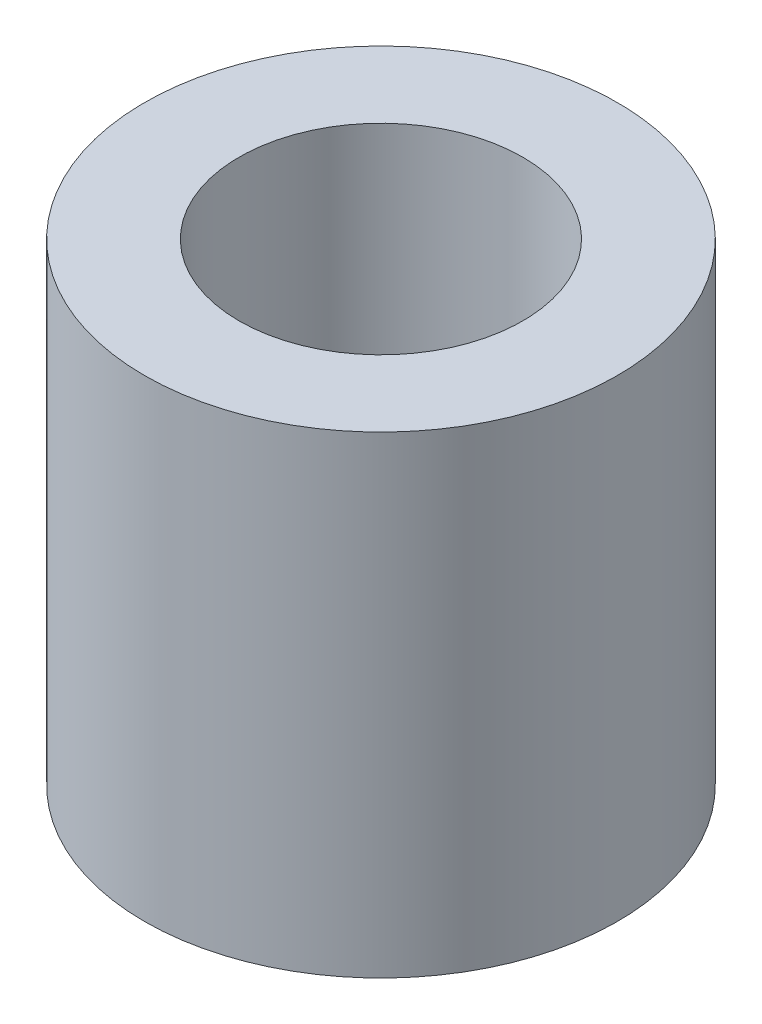
SolidWorks part; units mm, degrees
material "Brass"
ref_plane "Front Plane" through (0, 0, 0) normal (0, 0, 1) x (1, 0, 0)
ref_plane "Top Plane" through (0, 0, 0) normal (0, 1, 0) x (1, 0, 0)
ref_plane "Right Plane" through (0, 0, 0) normal (1, 0, 0) x (0, 0, -1)
sketch "Sketch1" plane through (0, 0, 0) normal (0, 1, 0) x (1, 0, 0)
  circle A0 centre (0, 0) radius 1.5
  circle A1 centre (0, 0) radius 2.5
  dimension "D1" = 1
  dimension "D2" = 5
extrude "Boss-Extrude1" add sketch "Sketch1" along normal blind 5
